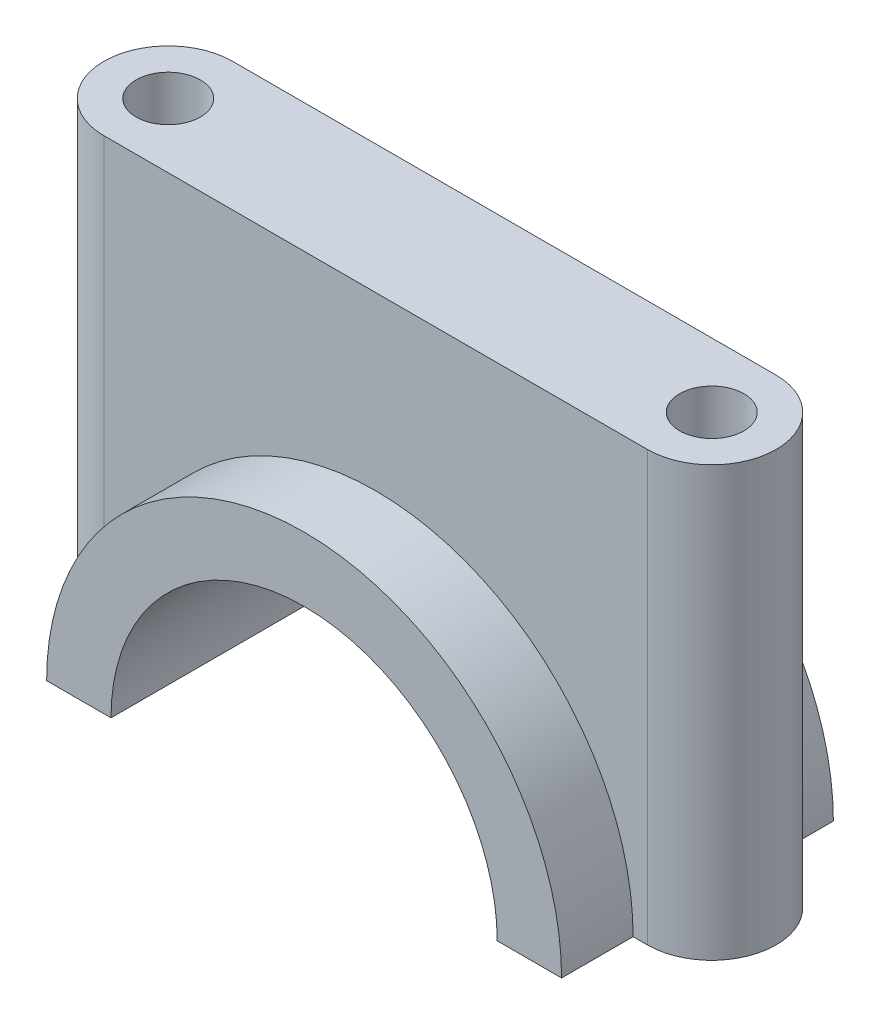
SolidWorks part; units mm, degrees
ref_plane "Front Plane" through (0, 0, 0) normal (0, 0, 1) x (1, 0, 0)
ref_plane "Top Plane" through (0, 0, 0) normal (0, 1, 0) x (1, 0, 0)
ref_plane "Right Plane" through (0, 0, 0) normal (1, 0, 0) x (0, 0, -1)
sketch "Sketch1" plane through (0, 0, 0) normal (0, 0, 1) x (1, 0, 0)
  line L0 (-36, 0) -> (-27, 0)
  line L1 (27, 0) -> (36, 0)
  arc A0 (27, 0) -> (-27, 0) centre (0, 0) ccw
  arc A1 (36, 0) -> (-36, 0) centre (0, 0) ccw
  dimension "D1" = 54
  dimension "D2" = 72
extrude "Boss-Extrude1" add sketch "Sketch1" along normal mid plane 38
ref_plane "Plane1" through (0, 60, 0) normal (0, -1, 0) x (-1, 0, 0)
sketch "Sketch2" plane through (0, 60, 0) normal (0, -1, 0) x (-1, 0, 0)
  line L0 (-38, 0) -> (38, 0) construction
  line L1 (-38, 9) -> (38, 9)
  line L2 (-38, -9) -> (38, -9)
  arc A0 (-38, 9) -> (-38, -9) centre (-38, 0) ccw
  arc A1 (38, -9) -> (38, 9) centre (38, 0) ccw
  point P2 (0, 0)
  dimension "D1" = 9
  dimension "D2" = 76
extrude "Boss-Extrude2" add sketch "Sketch2" along normal up to surface (60 mm away) up to face at (-31.5, 0, 0)
sketch "Sketch3" plane through (0, 0, 9) normal (0, 0, 1) x (1, 0, 0)
  line L1 (-27, 0) -> (27, 0)
  line L2 (-27, 0) -> (27, 0)
  arc A1 (27, 0) -> (-27, 0) centre (0, 0) ccw
  arc A2 (27, 0) -> (-27, 0) centre (0, 0) ccw
  dimension "D1" = 0
extrude "Cut-Extrude1" cut sketch "Sketch3" against normal through all
sketch "Sketch4" plane through (0, 0, 0) normal (0, -1, 0) x (1, 0, 0)
  circle A0 centre (-38, 0) radius 4.5
  circle A1 centre (38, 0) radius 4.5
  dimension "D1" = 9
  dimension "D2" = 9
extrude "Cut-Extrude2" cut sketch "Sketch4" against normal through all
